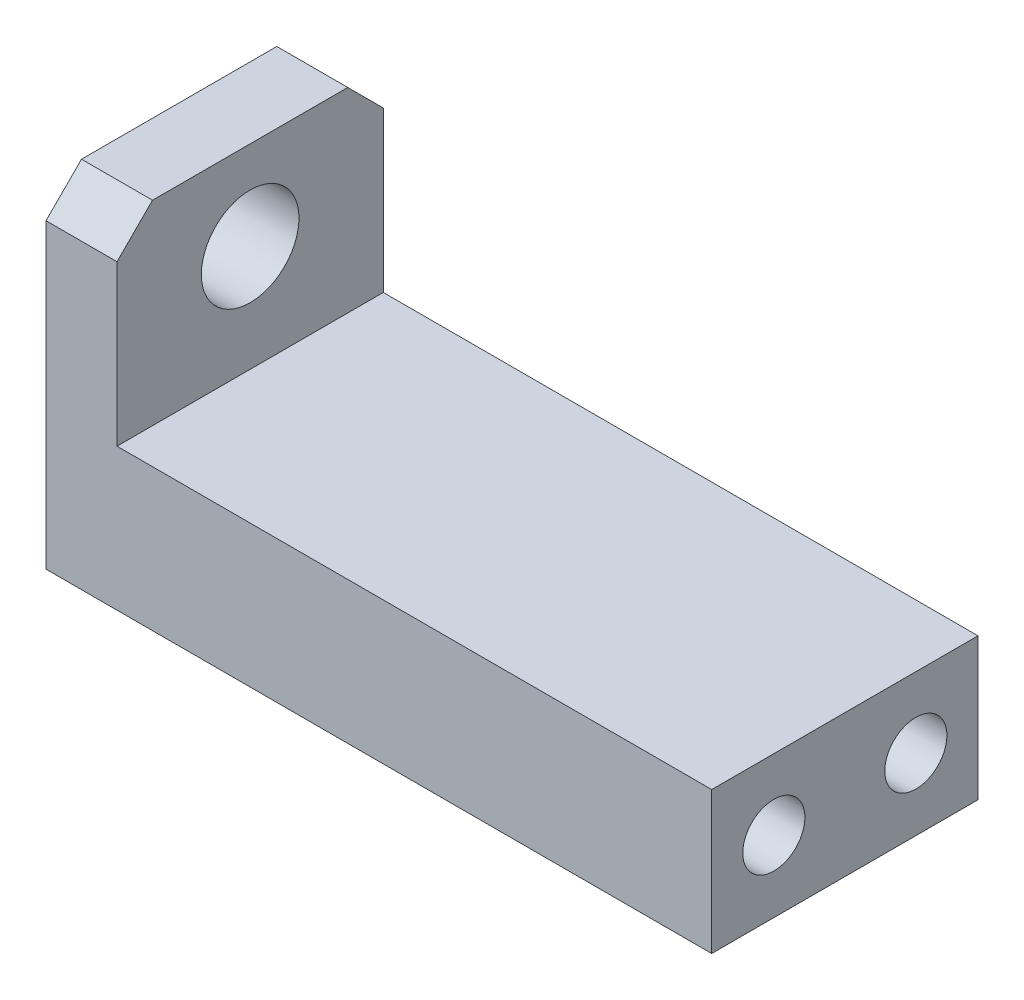
SolidWorks part; units mm, degrees
ref_plane "Front Plane" through (0, 0, 0) normal (0, 0, 1) x (1, 0, 0)
ref_plane "Top Plane" through (0, 0, 0) normal (0, 1, 0) x (1, 0, 0)
ref_plane "Right Plane" through (0, 0, 0) normal (1, 0, 0) x (0, 0, -1)
sketch "Sketch1" plane through (0, 0, 0) normal (0, 0, 1) x (1, 0, 0)
  line L0 (-12.1637, 2.0602) -> (-8.1637, 2.0602)
  line L1 (-8.1637, 2.0602) -> (-8.1637, -8.9398)
  line L2 (-8.1637, -8.9398) -> (25.3363, -8.9398)
  line L3 (25.3363, -8.9398) -> (25.3363, -16.9398)
  line L4 (25.3363, -16.9398) -> (-12.1637, -16.9398)
  line L5 (-12.1637, -16.9398) -> (-12.1637, 2.0602)
  dimension "D1" = 4
  dimension "D2" = 11
  dimension "D3" = 19
  dimension "D4" = 37.5
extrude "Boss-Extrude1" add sketch "Sketch1" along normal blind 15
sketch "Sketch2" plane through (-12.1637, 0, 0) normal (-1, 0, 0) x (0, 0, 1)
  line L0 (15, 2.0602) -> (0, 2.0602) construction
  line L1 (0, 2.0602) -> (0, -16.9398) construction
  line L2 (15, 2.0602) -> (0, 2.0602) construction
  circle A0 centre (7.5, -2.9398) radius 2.75
  circle A1 centre (3.5, -12.9147) radius 1.75
  circle A2 centre (11.5, -12.9147) radius 1.75
  circle A3 centre (11.5, -12.9147) radius 3
  circle A4 centre (3.5, -12.9147) radius 3
  point P8 (0, 0)
  point P9 (0, 0)
  point P10 (0, 0)
  point P13 (7.5, 2.0602)
  dimension "D1" = 3.5
  dimension "D2" = 6
  dimension "D4" = 8
  dimension "D5" = 5.5
  dimension "D3" = 3.5
  dimension "D6" = 5
extrude "Cut-Extrude1" cut sketch "Sketch2" against normal blind 15
sketch "Sketch3" plane through (-12.1637, 0, 0) normal (-1, 0, 0) x (0, 0, 1)
  circle A0 centre (3.5, -12.9147) radius 1.75
  circle A1 centre (11.5, -12.9147) radius 1.75
extrude "Cut-Extrude2" cut sketch "Sketch3" against normal through all
chamfer "Chamfer1" distance 2 angle 45 2 edges at (-10.1637, 2.0602, 0) (-10.1637, 2.0602, 15)
